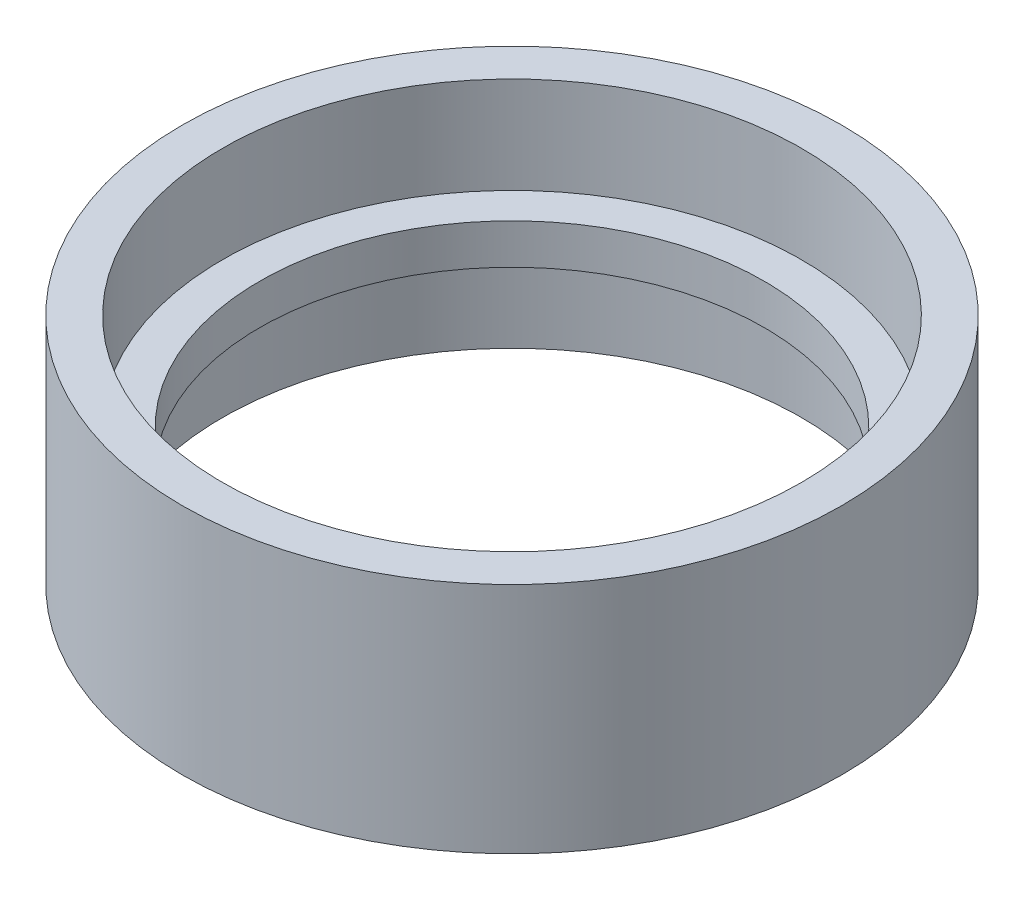
SolidWorks part; units mm, degrees
material "AISI 1020"
ref_plane "Спереди" through (0, 0, 0) normal (0, 0, 1) x (1, 0, 0)
ref_plane "Сверху" through (0, 0, 0) normal (0, 1, 0) x (1, 0, 0)
ref_plane "Справа" through (0, 0, 0) normal (1, 0, 0) x (0, 0, -1)
sketch "Эскиз1" plane through (0, 0, 0) normal (0, 0, 1) x (1, 0, 0)
  line L0 (-36, 15) -> (-36, 3)
  line L1 (-41, 32) -> (-36, 32)
  line L2 (-41, 32) -> (-41, 3)
  line L3 (-41, 3) -> (-36, 3)
  line L4 (-36, 32) -> (-36, 20)
  line L5 (-36, 20) -> (-31.374, 20)
  line L7 (-36, 15) -> (-31.374, 15)
  line L8 (-31.374, 20) -> (-31.374, 15)
  line L9 (35.4, 15) -> (-35.4, 15) construction
  line L10 (-35.4, 20) -> (35.4, 20) construction
  line L11 (36, 32) -> (-36, 32) construction
  line L12 (0, -1000) -> (0, 49000) construction
  dimension "D1" = 5
revolve "Повернуть1" add sketch "Эскиз1" angle 360 about L12
